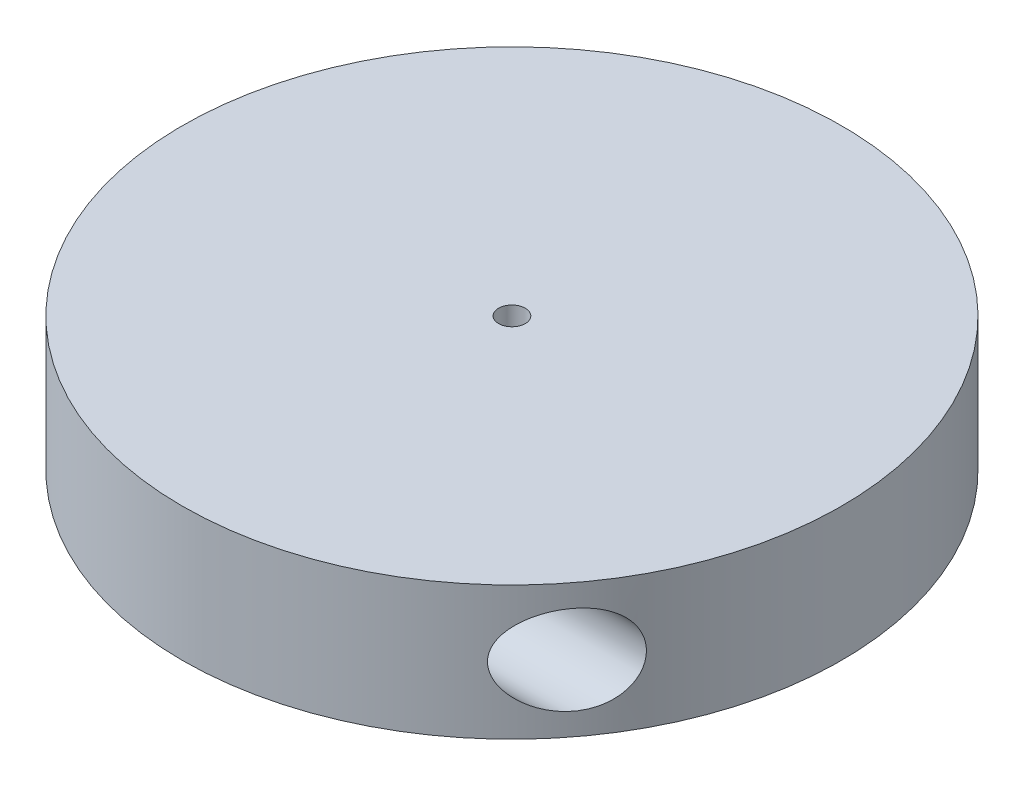
SolidWorks part; units mm, degrees
ref_plane "Front Plane" through (0, 0, 0) normal (0, 0, 1) x (1, 0, 0)
ref_plane "Top Plane" through (0, 0, 0) normal (0, 1, 0) x (1, 0, 0)
ref_plane "Right Plane" through (0, 0, 0) normal (1, 0, 0) x (0, 0, -1)
sketch "Sketch1" plane through (0, 0, 0) normal (0, 1, 0) x (1, 0, 0)
  circle A0 centre (0, 0) radius 74
extrude "Boss-Extrude1" add sketch "Sketch1" along normal blind 30
sketch "Sketch2" plane through (0, 0, 0) normal (1, 0, 0) x (0, 0, -1)
  circle A0 centre (45, 15) radius 10
extrude "Cut-Extrude1" cut sketch "Sketch2" against normal blind 80
sketch "Sketch3" plane through (0, 0, 0) normal (1, 0, 0) x (0, 0, -1)
  circle A0 centre (-45, 15) radius 10
extrude "Cut-Extrude2" cut sketch "Sketch3" along normal blind 80
sketch "Sketch6" plane through (0, 30, 0) normal (0, 1, 0) x (1, 0, 0)
  circle A0 centre (0, 0) radius 3
extrude "Cut-Extrude4" cut sketch "Sketch6" against normal blind 30
scale "Scale1" scale about centroid uniform scaling yes scale factor 0.75
